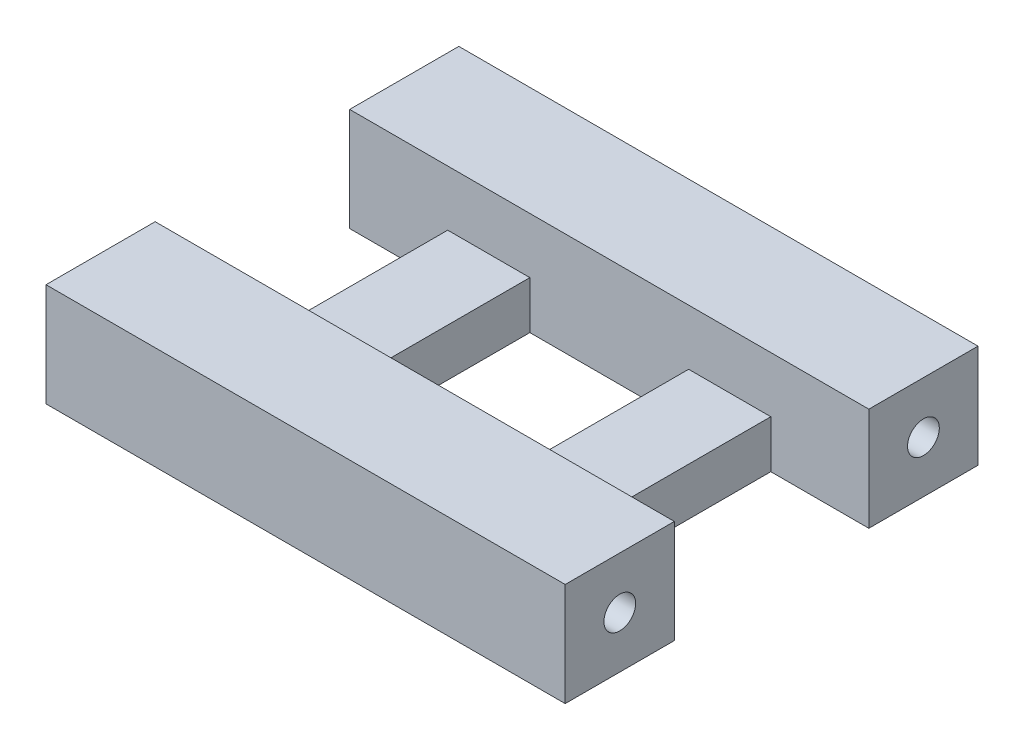
SolidWorks part; units mm, degrees
ref_plane "Alzado" through (0, 0, 0) normal (0, 0, 1) x (1, 0, 0)
ref_plane "Planta" through (0, 0, 0) normal (0, 1, 0) x (1, 0, 0)
ref_plane "Vista lateral" through (0, 0, 0) normal (1, 0, 0) x (0, 0, -1)
sketch "Croquis1" plane through (0, 0, 0) normal (0, 1, 0) x (1, 0, 0)
  line L0 (-15.6068, 13.6193) -> (-15.6068, 6.7443)
  line L1 (-15.6068, 6.7443) -> (-9.4318, 6.7443)
  line L2 (-9.4318, 6.7443) -> (-9.4318, -5.5057)
  line L3 (-9.4318, -5.5057) -> (-15.6068, -5.5057)
  line L4 (-15.6068, -5.5057) -> (-15.6068, -12.3807)
  line L5 (-15.6068, -12.3807) -> (17.0932, -12.3807)
  line L6 (17.0932, -12.3807) -> (17.0932, -5.5057)
  line L7 (17.0932, -5.5057) -> (10.9182, -5.5057)
  line L8 (10.9182, -5.5057) -> (10.9182, 6.7443)
  line L9 (10.9182, 6.7443) -> (17.0932, 6.7443)
  line L10 (17.0932, 6.7443) -> (17.0932, 13.6193)
  line L11 (17.0932, 13.6193) -> (-15.6068, 13.6193)
  line L12 (-4.2568, 6.7443) -> (5.7432, 6.7443)
  line L13 (-4.2568, 6.7443) -> (-4.2568, -5.5057)
  line L14 (-4.2568, -5.5057) -> (5.7432, -5.5057)
  line L15 (5.7432, 6.7443) -> (5.7432, -5.5057)
extrude "Saliente-Extruir1" add sketch "Croquis1" along normal blind 6.5
sketch "Croquis3" plane through (-15.6068, 0, 0) normal (-1, 0, 0) x (0, 0, 1)
  line L0 (5.5057, 6.5) -> (5.5057, 0) construction
  line L1 (-6.7443, 6.5) -> (5.5057, 6.5)
  line L2 (-6.7443, 6.5) -> (-6.7443, 3)
  line L3 (-6.7443, 3) -> (5.5057, 3)
  line L4 (5.5057, 6.5) -> (5.5057, 3)
  circle A0 centre (-10.1818, 3.25) radius 1
  circle A1 centre (8.9432, 3.25) radius 1
  dimension "D1" = 2
  dimension "D2" = 3.5
extrude "Cortar-Extruir1" cut sketch "Croquis3" against normal blind 35.4
